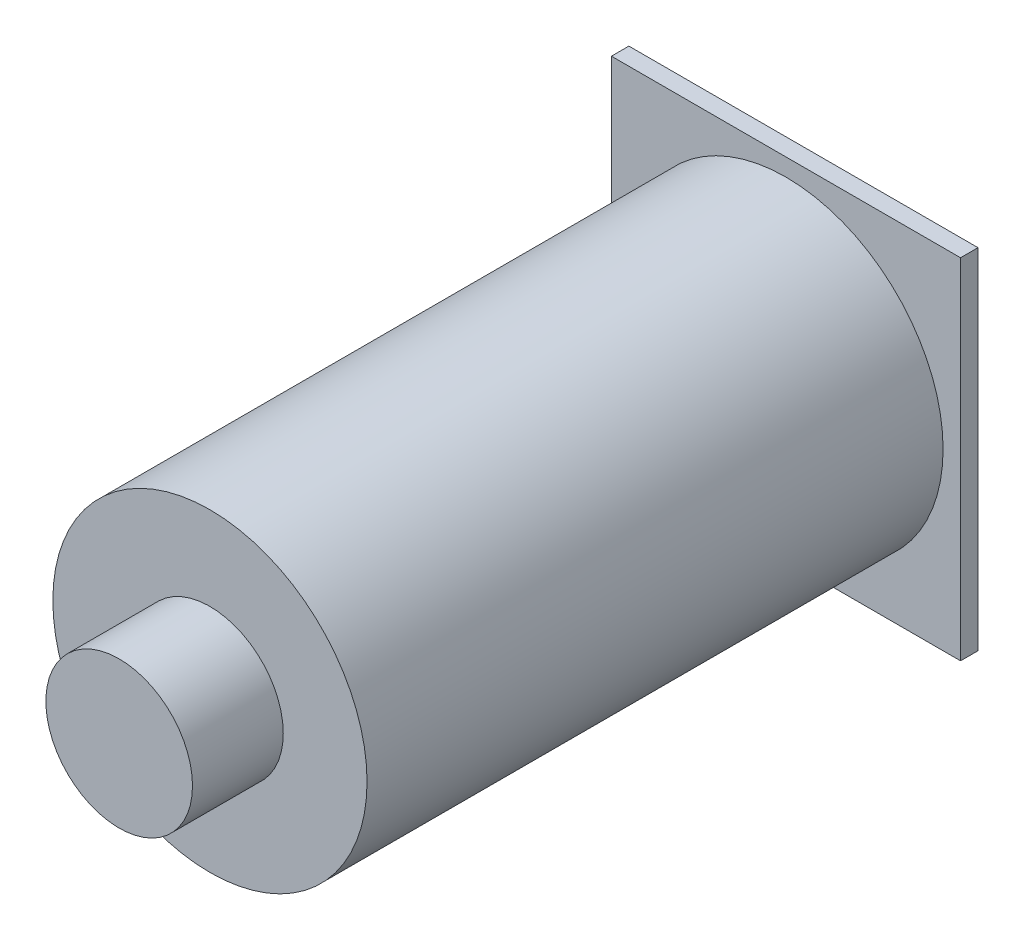
SolidWorks part; units mm, degrees
ref_plane "Front Plane" through (0, 0, 0) normal (0, 0, 1) x (1, 0, 0)
ref_plane "Top Plane" through (0, 0, 0) normal (0, 1, 0) x (1, 0, 0)
ref_plane "Right Plane" through (0, 0, 0) normal (1, 0, 0) x (0, 0, -1)
sketch "Sketch1" plane through (0, 0, 0) normal (0, 0, 1) x (1, 0, 0)
  line L1 (-63.5, -63.5) -> (63.5, -63.5)
  line L2 (-63.5, -63.5) -> (-63.5, 63.5)
  line L3 (-63.5, 63.5) -> (63.5, 63.5)
  line L4 (63.5, -63.5) -> (63.5, 63.5)
  line L5 (-63.5, -63.5) -> (63.5, 63.5) construction
  line L6 (-63.5, 63.5) -> (63.5, -63.5) construction
  point P0 (0, 0)
  dimension "D1" = 127
extrude "Boss-Extrude1" add sketch "Sketch1" along normal blind 6.35
sketch "Sketch2" plane through (0, 0, 6.35) normal (0, 0, 1) x (1, 0, 0)
  circle A0 centre (0, 0) radius 57.15
  dimension "D1" = 114.3
extrude "Boss-Extrude2" add sketch "Sketch2" along normal blind 209.55
sketch "Sketch3" plane through (0, 0, 215.9) normal (0, 0, 1) x (1, 0, 0)
  circle A0 centre (0, 0) radius 26.67
  dimension "D1" = 53.34
extrude "Boss-Extrude3" add sketch "Sketch3" along normal blind 33.02
